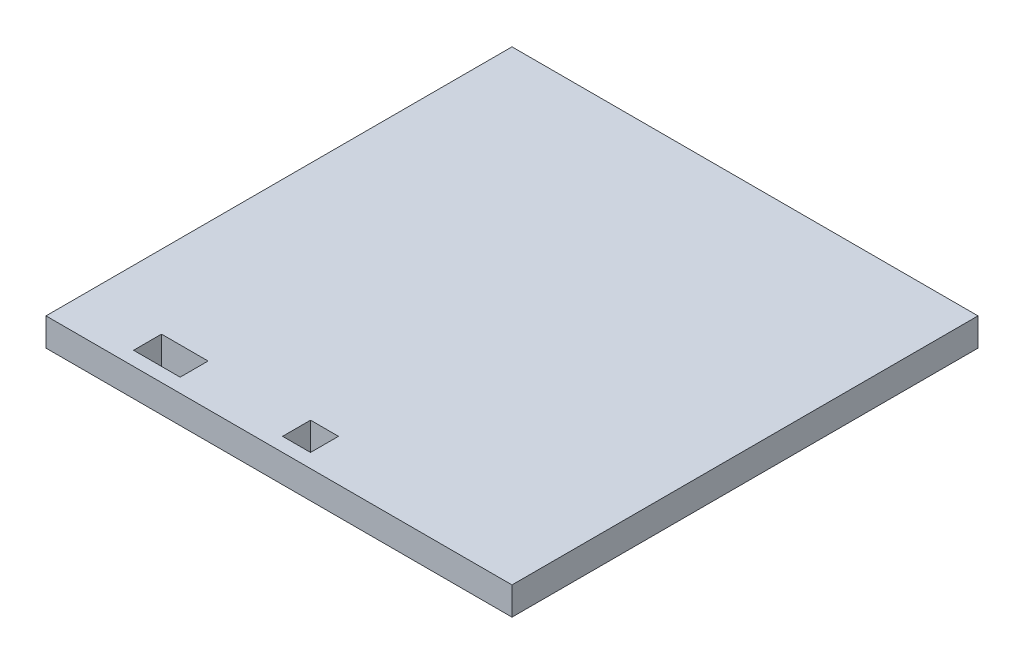
SolidWorks part; units mm, degrees
material "Maple"
ref_plane "Front Plane" through (0, 0, 0) normal (0, 0, 1) x (1, 0, 0)
ref_plane "Top Plane" through (0, 0, 0) normal (0, 1, 0) x (1, 0, 0)
ref_plane "Right Plane" through (0, 0, 0) normal (1, 0, 0) x (0, 0, -1)
sketch "Sketch1" plane through (0, 0, 0) normal (0, 1, 0) x (1, 0, 0)
  line L1 (-50, 50) -> (50, 50)
  line L2 (-50, 50) -> (-50, -50)
  line L3 (-50, -50) -> (50, -50)
  line L4 (50, 50) -> (50, -50)
  line L5 (-50, 50) -> (50, -50) construction
  line L6 (-50, -50) -> (50, 50) construction
  point P0 (0, 0)
  dimension "D1" = 100
extrude "Boss-Extrude1" add sketch "Sketch1" along normal blind 6
ref_plane "Plane1" through (0, 3, 0) normal (0, 1, 0) x (1, 0, 0)
sketch3d "3DSketch1"
  line L0 (-50, 6, 50) -> (50, 6, 50) construction
  point P0 (0.7678, 6, 44)
  point P3 (-29.2132, 6, 44)
  dimension "D1" = 6
  dimension "D2" = 6
sketch "Sketch6" plane through (0, 3, 0) normal (0, 1, 0) x (1, 0, 0)
  line L1 (-2.2322, -41) -> (3.7678, -41)
  line L2 (-2.2322, -41) -> (-2.2322, -47)
  line L3 (-2.2322, -47) -> (3.7678, -47)
  line L4 (3.7678, -41) -> (3.7678, -47)
  line L5 (-2.2322, -41) -> (3.7678, -47) construction
  line L6 (-2.2322, -47) -> (3.7678, -41) construction
  point P0 (0.7678, -44)
  dimension "slot_width" = 6
  dimension "D2" = 6
extrude "Cut-Extrude1" cut sketch "Sketch6" against normal through all and the other way through all
sketch "Sketch62" plane through (-28.4454, 3, 88) normal (0, 1, 0) x (-1, 0, 0)
  line L1 (-4.2322, -41) -> (5.7678, -41)
  line L2 (-4.2322, -41) -> (-4.2322, -47)
  line L3 (-4.2322, -47) -> (5.7678, -47)
  line L4 (5.7678, -41) -> (5.7678, -47)
  line L5 (-4.2322, -41) -> (5.7678, -47) construction
  line L6 (-4.2322, -47) -> (5.7678, -41) construction
  point P0 (0.7678, -44)
  dimension "D1" = 10
  dimension "D2" = 6
extrude "Cut-Extrude12" cut sketch "Sketch62" against normal through all and the other way through all
other "Smart-Feature2<virtual_pin-3>"
